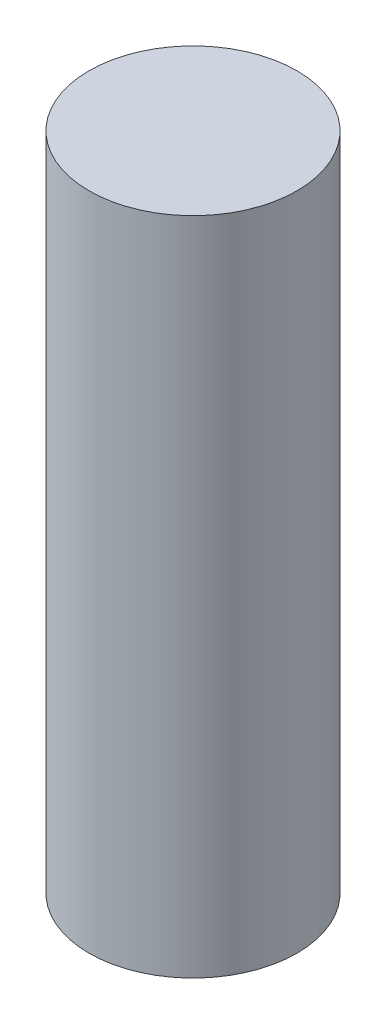
SolidWorks part; units mm, degrees
ref_plane "Front Plane" through (0, 0, 0) normal (0, 0, 1) x (1, 0, 0)
ref_plane "Top Plane" through (0, 0, 0) normal (0, 1, 0) x (1, 0, 0)
ref_plane "Right Plane" through (0, 0, 0) normal (1, 0, 0) x (0, 0, -1)
sketch "Sketch1" plane through (0, 0, 0) normal (0, 1, 0) x (1, 0, 0)
  circle A0 centre (0, 0) radius 2
  dimension "D1" = 4
extrude "dowel_body" add sketch "Sketch1" along normal blind 12.7
